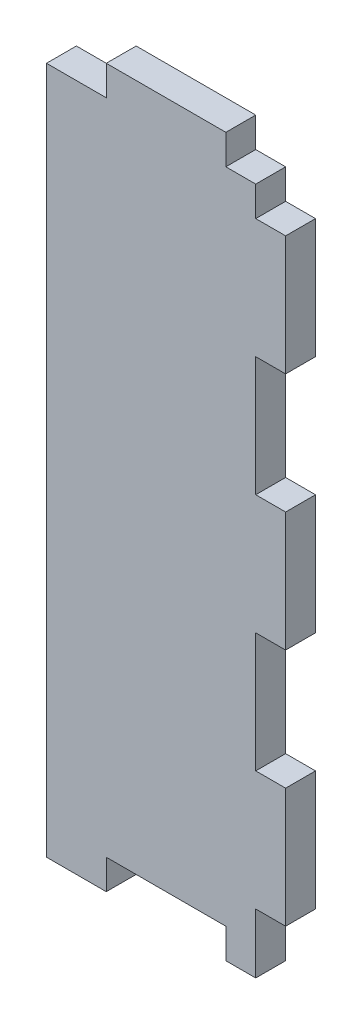
SolidWorks part; units mm, degrees
ref_plane "Front Plane" through (0, 0, 0) normal (0, 0, 1) x (1, 0, 0)
ref_plane "Top Plane" through (0, 0, 0) normal (0, 1, 0) x (1, 0, 0)
ref_plane "Right Plane" through (0, 0, 0) normal (1, 0, 0) x (0, 0, -1)
sketch "Sketch1" plane through (0, 0, 0) normal (0, 0, 1) x (1, 0, 0)
  line L1 (0, 0) -> (25.4, 0)
  line L2 (0, 0) -> (0, 76.2)
  line L3 (0, 76.2) -> (25.4, 76.2)
  line L4 (25.4, 0) -> (25.4, 76.2)
  dimension "D1" = 76.2
  dimension "D2" = 25.4
extrude "Extrude1" add sketch "Sketch1" along normal blind 3.175
sketch "Sketch3" plane through (0, 0, 3.175) normal (0, 0, 1) x (1, 0, 0)
  line L0 (25.4, 0) -> (25.4, 76.2) construction
  line L1 (25.4, 69.85) -> (22.225, 69.85)
  line L2 (25.4, 69.85) -> (25.4, 76.2)
  line L3 (25.4, 76.2) -> (22.225, 76.2)
  line L4 (22.225, 69.85) -> (22.225, 76.2)
  dimension "D1" = 6.35
  dimension "D2" = 3.175
  dimension "D3" = 6.35
extrude "Cut-Extrude1" cut sketch "Sketch3" against normal blind 3.175
pattern_linear "LPattern1" count 3 spacing 69.85 along (0, -1, 0) of "Cut-Extrude1"
sketch "Sketch4" plane through (0, 0, 3.175) normal (0, 0, 1) x (1, 0, 0)
  line L0 (25.4, 6.35) -> (25.4, 69.85) construction
  line L1 (25.4, 57.15) -> (22.225, 57.15)
  line L2 (25.4, 57.15) -> (25.4, 44.45)
  line L3 (25.4, 44.45) -> (22.225, 44.45)
  line L4 (22.225, 57.15) -> (22.225, 44.45)
  line L5 (22.225, 76.2) -> (0, 76.2) construction
  dimension "D1" = 12.7
  dimension "D2" = 3.175
  dimension "D3" = 19.05
extrude "Cut-Extrude2" cut sketch "Sketch4" against normal blind 3.175
pattern_linear "LPattern2" count 2 spacing 25.4 along (0, -1, 0) of "Cut-Extrude2"
sketch "Sketch5" plane through (0, 0, 3.175) normal (0, 0, 1) x (1, 0, 0)
  line L0 (0, 0) -> (22.225, 0) construction
  line L1 (19.05, 0) -> (6.35, 0)
  line L2 (19.05, 0) -> (19.05, 3.175)
  line L3 (19.05, 3.175) -> (6.35, 3.175)
  line L4 (6.35, 0) -> (6.35, 3.175)
  dimension "D1" = 6.35
  dimension "D2" = 12.7
  dimension "D3" = 3.175
extrude "Cut-Extrude3" cut sketch "Sketch5" against normal blind 3.175
sketch "Sketch6" plane through (0, 0, 3.175) normal (0, 0, 1) x (1, 0, 0)
  line L1 (0, 76.2) -> (6.35, 76.2)
  line L2 (0, 76.2) -> (0, 73.025)
  line L3 (0, 73.025) -> (6.35, 73.025)
  line L4 (6.35, 76.2) -> (6.35, 73.025)
  dimension "D1" = 6.35
  dimension "D2" = 3.175
extrude "Cut-Extrude4" cut sketch "Sketch6" against normal blind 3.175
pattern_linear "LPattern3" count 2 spacing 19.05 along (1, 0, 0) of "Cut-Extrude4"
